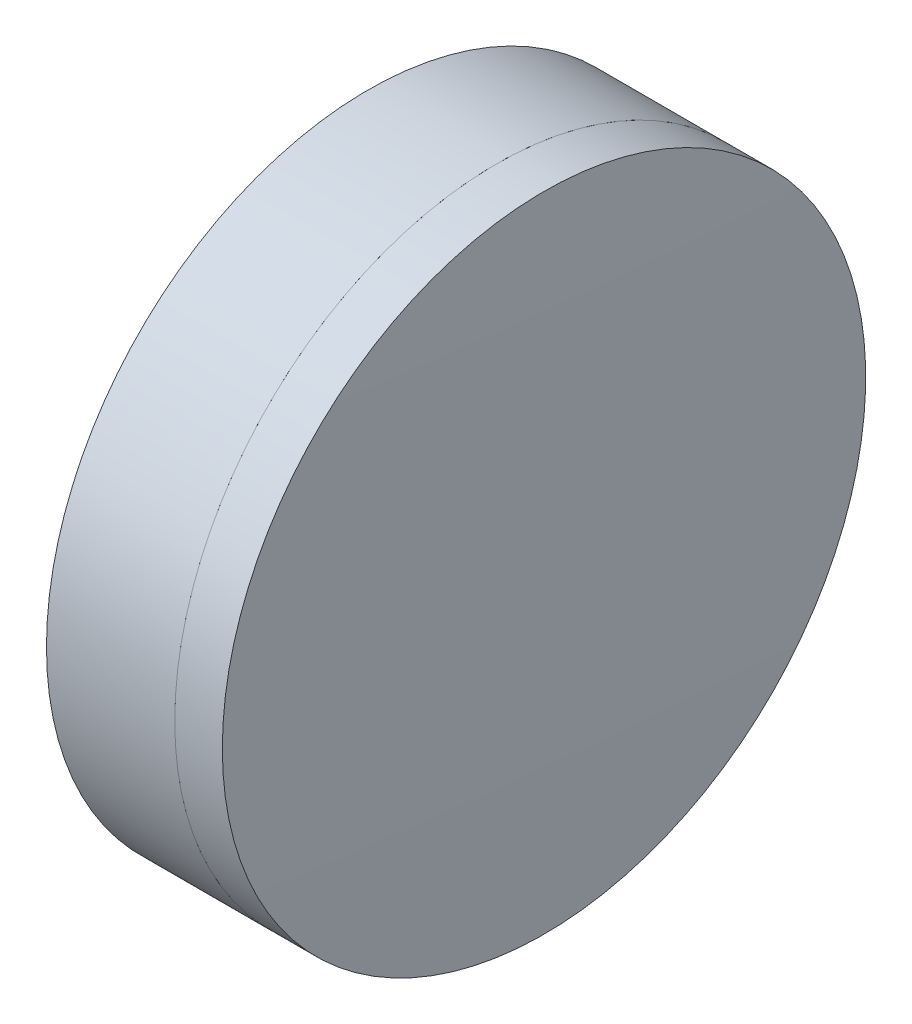
SolidWorks part; units mm, degrees
ref_plane "前视基准面" through (0, 0, 0) normal (0, 0, 1) x (1, 0, 0)
ref_plane "上视基准面" through (0, 0, 0) normal (0, 1, 0) x (1, 0, 0)
ref_plane "右视基准面" through (0, 0, 0) normal (1, 0, 0) x (0, 0, -1)
sketch "草图1" plane through (0, 0, 0) normal (0, 1, 0) x (1, 0, 0)
  line L0 (-185.2745, 0) -> (373.252, 0) construction
  line L1 (141.1072, 12.7) -> (146.1718, 12.7)
  line L4 (141.1072, -12.7) -> (146.1718, -12.7)
  arc A0 (141.1072, -12.7) -> (141.1072, 12.7) centre (93.9888, 0) ccw
  arc A1 (146.1718, 12.7) -> (146.1718, -12.7) centre (203.7888, 0) ccw
  point P6 (142.7888, 0)
  point P8 (144.7888, 0)
  dimension "D3" = 12.7
  dimension "D4" = 2
  dimension "D1" = 48.8
  dimension "D5" = 59
  dimension "D2" = 12.7
revolve "旋转1" add sketch "草图1" angle 360 about L0
sketch "草图2" plane through (0, 0, 0) normal (0, 1, 0) x (1, 0, 0)
  line L2 (141.1072, 0) -> (272.9951, 0) construction
  line L3 (141.1072, -12.7) -> (141.1072, 12.7) construction
  line L6 (146.1718, 12.7) -> (148.0499, 12.7)
  line L7 (146.1718, -12.7) -> (148.0499, -12.7)
  arc A0 (148.0499, -12.7) -> (148.0499, 12.7) centre (-432.6112, 0) ccw
  arc A2 (146.1718, 12.7) -> (146.1718, -12.7) centre (203.7888, 0) ccw construction
  arc A3 (146.1718, 12.7) -> (146.1718, -12.7) centre (203.7888, 0) ccw
  point P8 (144.7888, 0)
  point P15 (148.1888, 0)
  dimension "D1" = 580.8
  dimension "D2" = 3.4
revolve "旋转3" add sketch "草图2" angle 360 about L2
